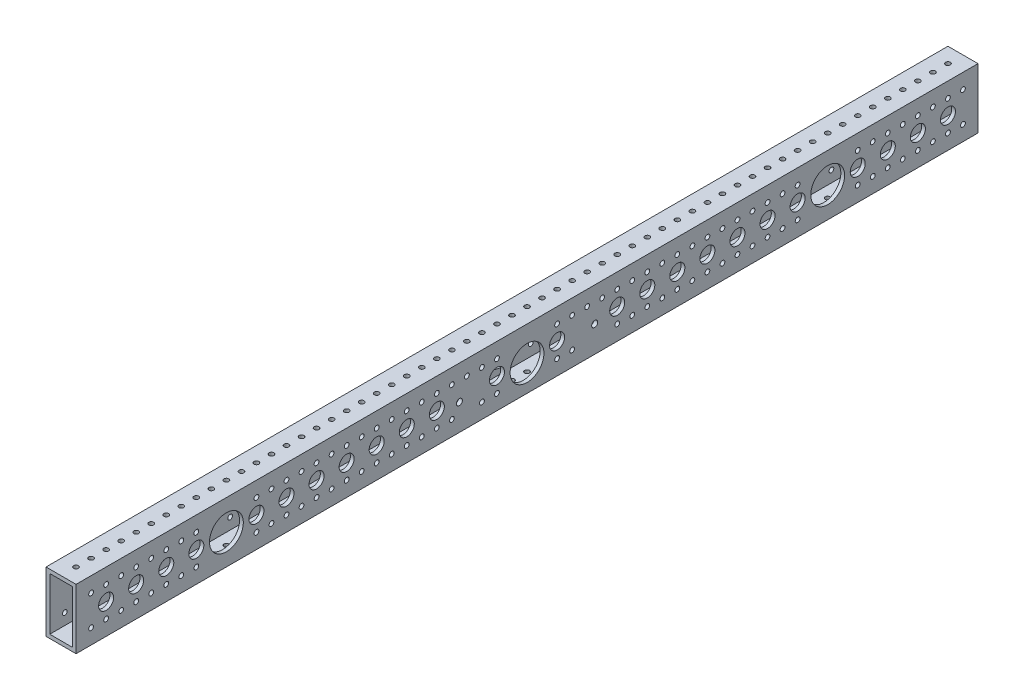
SolidWorks part; units mm, degrees
material "6061 Alloy"
ref_plane "Front Plane" through (0, 0, 0) normal (0, 0, 1) x (1, 0, 0)
ref_plane "Top Plane" through (0, 0, 0) normal (0, 1, 0) x (1, 0, 0)
ref_plane "Right Plane" through (0, 0, 0) normal (1, 0, 0) x (0, 0, -1)
sketch "Sketch1" plane through (0, 0, 0) normal (0, 0, 1) x (1, 0, 0)
  line L1 (12.7, 25.4) -> (-12.7, 25.4)
  line L2 (12.7, 25.4) -> (12.7, -25.4)
  line L3 (12.7, -25.4) -> (-12.7, -25.4)
  line L4 (-12.7, 25.4) -> (-12.7, -25.4)
  line L5 (12.7, 25.4) -> (-12.7, -25.4) construction
  line L6 (12.7, -25.4) -> (-12.7, 25.4) construction
  point P0 (0, 0)
  dimension "D1" = 25.4
  dimension "D2" = 50.8
extrude "Boss-Extrude1" add sketch "Sketch1" along normal blind 762
shell "Shell1" thickness 3.175
hole_wizard "#21 (0.159) Diameter Hole1" positions "Sketch2" profile "Sketch3" hole size "#21" standard "ANSI Inch" end condition through all
sketch "Sketch2" plane through (0, 25.4, 0) normal (0, 1, 0) x (1, 0, 0)
  line L0 (12.7, 0) -> (-12.7, 0) construction
  line L1 (12.7, -762) -> (12.7, 0) construction
  point P0 (0, -12.7)
  dimension "D1" = 12.7
  dimension "D2" = 12.7
sketch "Sketch3" plane through (0, 25.4, 12.7) normal (1, 0, 0) x (0, 0, 1)
  line L0 (0, 0) -> (0, 50.8)
  line L1 (0, 50.8) -> (2.0193, 50.8)
  line L2 (2.0193, 50.8) -> (2.0193, 0)
  line L5 (2.0193, 0) -> (0, 0)
  line L11 (0, -6.35) -> (0, 107.95) construction
  dimension "Thru Hole Dia." = 4.0386
  dimension "Thru Hole Depth" = 50.8
pattern_linear "LPattern1" count 59 spacing 12.7 along (0, 0, 1) of "#21 (0.159) Diameter Hole1"
hole_wizard "#21 (0.159) Diameter Hole2" positions "Sketch4" profile "Sketch5" hole size "#21" standard "ANSI Inch" end condition through all
sketch "Sketch4" plane through (-12.7, 0, 0) normal (-1, 0, 0) x (0, 0, 1)
  line L0 (762, 25.4) -> (0, 25.4) construction
  line L1 (0, 25.4) -> (0, -25.4) construction
  point P0 (12.7, 12.7)
  dimension "D1" = 12.7
  dimension "D2" = 12.7
sketch "Sketch5" plane through (-12.7, 12.7, 12.7) normal (0, 1, 0) x (0, 0, 1)
  line L0 (0, 0) -> (0, 25.4)
  line L1 (0, 25.4) -> (2.0193, 25.4)
  line L2 (2.0193, 25.4) -> (2.0193, 0)
  line L5 (2.0193, 0) -> (0, 0)
  line L11 (0, -6.35) -> (0, 107.95) construction
  dimension "Thru Hole Dia." = 4.0386
  dimension "Thru Hole Depth" = 25.4
pattern_linear "LPattern2" count 59 spacing 12.7 along (0, 0, 1) count 2 spacing 25.4 along (0, -1, 0) skipping (8, 0), (8, 1), (9, 0), (9, 1), (10, 0), (10, 1), (24, 1), (25, 1), (28, 0), (28, 1), (29, 0), (29, 1), (30, 0), (30, 1), (33, 1), (48, 0), (48, 1), (49, 0), (49, 1), (50, 0), (50, 1) of "#21 (0.159) Diameter Hole2"
hole_wizard "1/2 (0.5) Diameter Hole1" positions "Sketch6" profile "Sketch7" hole size "1/2" standard "ANSI Inch" end condition through all
sketch "Sketch6" plane through (-12.7, 0, 0) normal (-1, 0, 0) x (0, 0, 1)
  line L0 (762, 25.4) -> (0, 25.4) construction
  line L1 (0, 25.4) -> (0, -25.4) construction
  point P0 (25.4, 0)
  dimension "D1" = 25.4
  dimension "D2" = 25.4
sketch "Sketch7" plane through (-12.7, 0, 25.4) normal (0, 1, 0) x (0, 0, 1)
  line L0 (0, 0) -> (0, 25.4)
  line L1 (0, 25.4) -> (6.35, 25.4)
  line L2 (6.35, 25.4) -> (6.35, 0)
  line L5 (6.35, 0) -> (0, 0)
  line L11 (0, -6.35) -> (0, 107.95) construction
  dimension "Thru Hole Dia." = 12.7
  dimension "Thru Hole Depth" = 25.4
pattern_linear "LPattern3" count 29 spacing 25.4 along (0, 0, 1) skipping (4, 0), (12, 0), (14, 0), (16, 0), (24, 0) of "1/2 (0.5) Diameter Hole1"
sketch "Sketch8" plane through (-12.7, 0, 0) normal (-1, 0, 0) x (0, 0, 1)
  line L0 (762, -25.4) -> (0, -25.4) construction
  line L1 (762, 25.4) -> (762, -25.4) construction
  line L2 (0, 25.4) -> (0, -25.4) construction
  line L3 (762, 25.4) -> (0, 25.4) construction
  point P0 (381, -3.175)
  point P5 (127, 0)
  point P6 (635, 0)
  dimension "D1" = 22.225
  dimension "D2" = 381
  dimension "D3" = 127
  dimension "D4" = 127
  dimension "D5" = 25.4
  dimension "D6" = 25.4
hole_wizard "1/2 (1.125) Diameter Hole1" positions "Sketch9" profile "Sketch10" hole size "1/2" standard "ANSI Inch" end condition through all
sketch "Sketch9" plane through (-12.7, 0, 0) normal (-1, 0, 0) x (0, 0, 1)
  point P0 (127, 0)
  point P3 (381, -3.175)
  point P6 (635, 0)
sketch "Sketch10" plane through (-12.7, 0, 127) normal (0, 1, 0) x (0, 0, 1)
  line L0 (0, 0) -> (0, 25.4)
  line L1 (0, 25.4) -> (14.2875, 25.4)
  line L2 (14.2875, 25.4) -> (14.2875, 0)
  line L5 (14.2875, 0) -> (0, 0)
  line L11 (0, -6.35) -> (0, 107.95) construction
  dimension "Thru Hole Dia." = 28.575
  dimension "Thru Hole Depth" = 25.4
sketch "Sketch11" plane through (-12.7, 0, 0) normal (-1, 0, 0) x (0, 0, 1)
  point P0 (438.15, -3.175)
  point P1 (323.85, -3.175)
  dimension "D1" = 57.15
  dimension "D2" = 57.15
hole_wizard "CBORE for #00 Binding Head Machine Screw1" positions "Sketch12" profile "Sketch14" counterbore size "#00" standard "ANSI Inch" end condition through all
sketch "Sketch12" plane through (-12.7, 0, 0) normal (-1, 0, 0) x (0, 0, 1)
  point P0 (323.85, -3.175)
  point P3 (438.15, -3.175)
sketch "Sketch14" plane through (-12.7, -3.175, 323.85) normal (0, 1, 0) x (0, 0, 1)
  line L0 (0, 0) -> (0, 25.4)
  line L1 (0, 25.4) -> (2.5527, 25.4)
  line L3 (2.5527, 25.4) -> (2.5527, 3.175)
  line L4 (2.5527, 3.175) -> (7.9375, 3.175)
  line L5 (7.9375, 3.175) -> (7.9375, 0)
  line L7 (7.9375, 0) -> (0, 0)
  line L11 (0, -6.35) -> (0, 107.95) construction
  dimension "Thru Hole Dia." = 5.1054
  dimension "Thru Hole Depth" = 25.4
  dimension "C'Bore Dia." = 15.875
  dimension "C'Bore Depth" = 3.175
equation "\"Length\"= 30"
equation "\"D1@Boss-Extrude1\"= \"Length\""
equation "\"D2@Sketch8\"= \"Length\" / 2"
